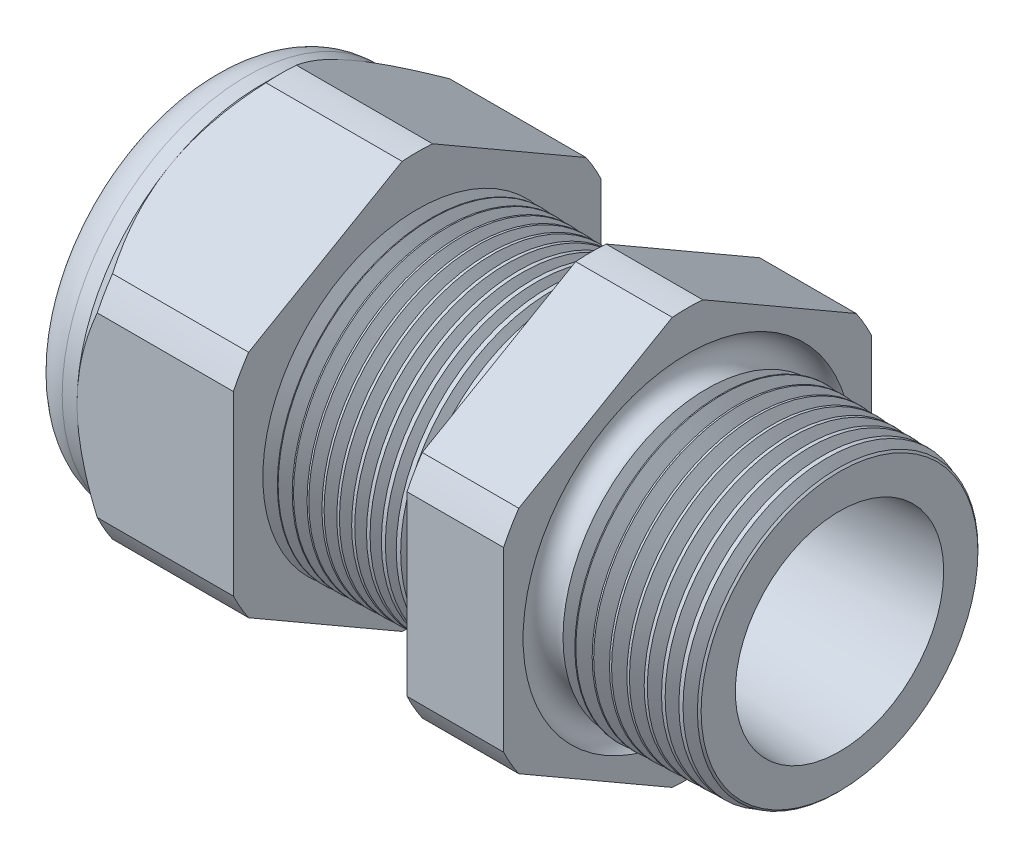
SolidWorks part; units mm, degrees
ref_plane "Front Plane" through (0, 0, 0) normal (0, 0, 1) x (1, 0, 0)
ref_plane "Top Plane" through (0, 0, 0) normal (0, 1, 0) x (1, 0, 0)
ref_plane "Right Plane" through (0, 0, 0) normal (1, 0, 0) x (0, 0, -1)
sketch "Sketch10" plane through (0, 0, 0) normal (0, 0, 1) x (1, 0, 0)
  line L0 (0, 0) -> (-115.3565, 0) construction
  line L1 (-32.766, 3.937) -> (-21.866, 3.937)
  line L2 (0, 5.3964) -> (0, 7.4284)
  line L3 (-7.874, 7.6346) -> (0, 7.4284)
  line L4 (-7.874, 19.05) -> (-7.874, 7.6346)
  line L5 (-7.874, 19.05) -> (-12.874, 19.05)
  line L6 (-12.874, 19.05) -> (-12.874, 7.7655)
  line L7 (-21.866, 8.001) -> (-12.874, 7.7655)
  line L8 (-21.866, 8.001) -> (-21.866, 19.05)
  line L9 (-21.866, 19.05) -> (-29.966, 19.05)
  line L10 (-29.966, 19.05) -> (-29.966, 9.525)
  line L11 (-29.966, 9.525) -> (-32.766, 9.525)
  line L12 (-32.766, 9.525) -> (-32.766, 3.937)
  line L13 (-21.866, 3.937) -> (0, 5.3964)
  dimension "D1" = 32.766
  dimension "D2" = 7.874
  dimension "D3" = 1.5
  dimension "D4" = 2.032
  dimension "A" = 16.002
  dimension "D6" = 19.05
  dimension "D8" = 38.1
  dimension "D9" = 2.8
  dimension "D10" = 8.1
  dimension "D11" = 5
  dimension "D" = 7.874
revolve "Revolve2" add sketch "Sketch10" angle 360 about L0
sketch "Sketch12" plane through (-29.966, 0, 0) normal (-1, 0, 0) x (0, 0, 1)
  line L1 (-0.7885, 10.5433) -> (-8.7365, 5.9545)
  line L2 (-9.525, 4.5888) -> (-9.525, -4.5888)
  line L3 (-8.7365, -5.9545) -> (-0.7885, -10.5433)
  line L4 (0.7885, -10.5433) -> (8.7365, -5.9545)
  line L5 (9.525, -4.5888) -> (9.525, 4.5888)
  line L6 (8.7365, 5.9545) -> (0.7885, 10.5433)
  circle A0 centre (0, 0) radius 9.525 construction
  arc A1 (0.7885, 10.5433) -> (-0.7885, 10.5433) centre (0, 0) ccw
  arc A2 (-8.7365, 5.9545) -> (-9.525, 4.5888) centre (0, 0) ccw
  arc A3 (-9.525, -4.5888) -> (-8.7365, -5.9545) centre (0, 0) ccw
  arc A4 (-0.7885, -10.5433) -> (0.7885, -10.5433) centre (0, 0) ccw
  arc A5 (8.7365, -5.9545) -> (9.525, -4.5888) centre (0, 0) ccw
  arc A6 (9.525, 4.5888) -> (8.7365, 5.9545) centre (0, 0) ccw
  dimension "D2" = 21.1455
  dimension "D1" = 19.05
extrude "Cut-Extrude2" cut sketch "Sketch12" against normal through all flip side to cut
fillet "Fillet4" radius 2.032 1 edges at (-32.766, 0, -9.525)
sketch "Sketch19" plane through (-29.966, 0, 0) normal (-1, 0, 0) x (0, 0, 1)
  line L0 (9.525, 0) -> (9.525, 4.5888) construction
  circle A0 centre (0, 0) radius 9.525
extrude "Cut-Extrude3" cut sketch "Sketch19" against normal blind 2 draft 45 flip side to cut
chamfer "Chamfer1" distance 0.254 angle 45 1 edges at (0, 0, -7.4284)
sketch "Sketch21" plane through (-32.766, 0, 0) normal (-1, 0, 0) x (0, 0, 1)
  circle A0 centre (0, 0) radius 3.937
  circle A2 centre (0, 0) radius 3.937 construction
extrude "plug" add sketch "Sketch21" against normal blind 3.81 separate body
sketch "Sketch22" plane through (-32.766, 0, 0) normal (-1, 0, 0) x (0, 0, 1)
  circle A0 centre (0, 0) radius 3.683
  circle A1 centre (0, 0) radius 3.937 construction
  dimension "D1" = 0.254
extrude "Cut-Extrude4" cut sketch "Sketch22" against normal blind 0.508
sketch "Sketch27" plane through (-32.258, 0, 0) normal (-1, 0, 0) x (0, 0, 1)
  line L0 (-4.3624, 0) -> (4.3624, 0) construction
  circle A0 centre (-2.7904, 0) radius 0.889
  circle A1 centre (0, 0) radius 3.683 construction
  dimension "D1" = 0.0036
  dimension "holedia" = 1.778
extrude "plugholes" cut sketch "Sketch27" against normal through all
pattern_circular "CirPattern1" count 3 over 360 about axis through (0, 0, 0) along (1, 0, 0) of "plugholes"
sketch "Sketch28" [suppressed] plane through (-29.464, 0, 0) normal (-1, 0, 0) x (0, 0, 1)
  circle A0 centre (0, 0) radius 0.762
  dimension "midholedia" = 1.778
extrude "midhole" [suppressed] cut sketch "Sketch28" against normal through all
sketch "Sketch29" plane through (0, 0, 0) normal (0, 0, 1) x (1, 0, 0)
  line L0 (-21.866, 8.001) -> (-21.133, 7.9818)
  line L1 (-12.874, 7.7655) -> (-21.866, 8.001) construction
  line L2 (-21.133, 7.9818) -> (-21.5161, 7.3566)
  line L3 (-21.5161, 7.3566) -> (-21.866, 8.001)
  dimension "D1" = 60
  dimension "D2" = 60
  dimension "D3" = 0.635
revolve "Cut-Revolve1" cut sketch "Sketch29" angle 360 about axis through (0, 0, 0) along (-1, 0, 0)
pattern_linear "LPattern1" count 12 spacing 0.762 along (1, 0, 0) of "Cut-Revolve1"
sketch "Sketch30" plane through (0, 0, 0) normal (0, 0, 1) x (1, 0, 0)
  line L0 (-7.874, 7.6346) -> (-6.9944, 7.6116)
  line L1 (-7.874, 10.5433) -> (-7.874, 5.9545) construction
  line L2 (-0.2539, 7.4351) -> (-7.874, 7.6346) construction
  line L3 (-6.9944, 7.6116) -> (-7.4542, 6.8614)
  line L4 (-7.4542, 6.8614) -> (-7.874, 7.6346)
  dimension "D1" = 60
  dimension "D2" = 60
  dimension "D3" = 0.762
revolve "Cut-Revolve2" cut sketch "Sketch30" angle 360 about axis through (0, 0, 0) along (-1, 0, 0)
pattern_linear "LPattern2" count 9 spacing 0.889 along (1, 0, 0) of "Cut-Revolve2"
sketch "Sketch31" [suppressed] plane through (-38.354, 0, 0) normal (-1, 0, 0) x (0, 0, 1)
  line L0 (-1.905, 1.905) -> (1.905, 1.905)
  line L1 (-1.905, -1.905) -> (1.905, -1.905)
  circle A0 centre (0, 0) radius 1.905 construction
  arc A1 (-1.905, 1.905) -> (-1.905, -1.905) centre (-1.905, 0) ccw
  arc A2 (1.905, 1.905) -> (1.905, -1.905) centre (1.905, 0) cw
extrude "Cut-Extrude5" [suppressed] cut sketch "Sketch31" against normal through all
sketch "Sketch32" plane through (0, 0, 0) normal (0, 0, 1) x (1, 0, 0)
  line L0 (-7.874, 10.5433) -> (-7.874, 5.9545) construction
  circle A0 centre (-7.747, 7.6346) radius 0.889
  dimension "D2" = 1.778
  dimension "D1" = 0.127
revolve "Cut-Revolve3" cut sketch "Sketch32" angle 360 about axis through (0, 0, 0) along (-1, 0, 0)
